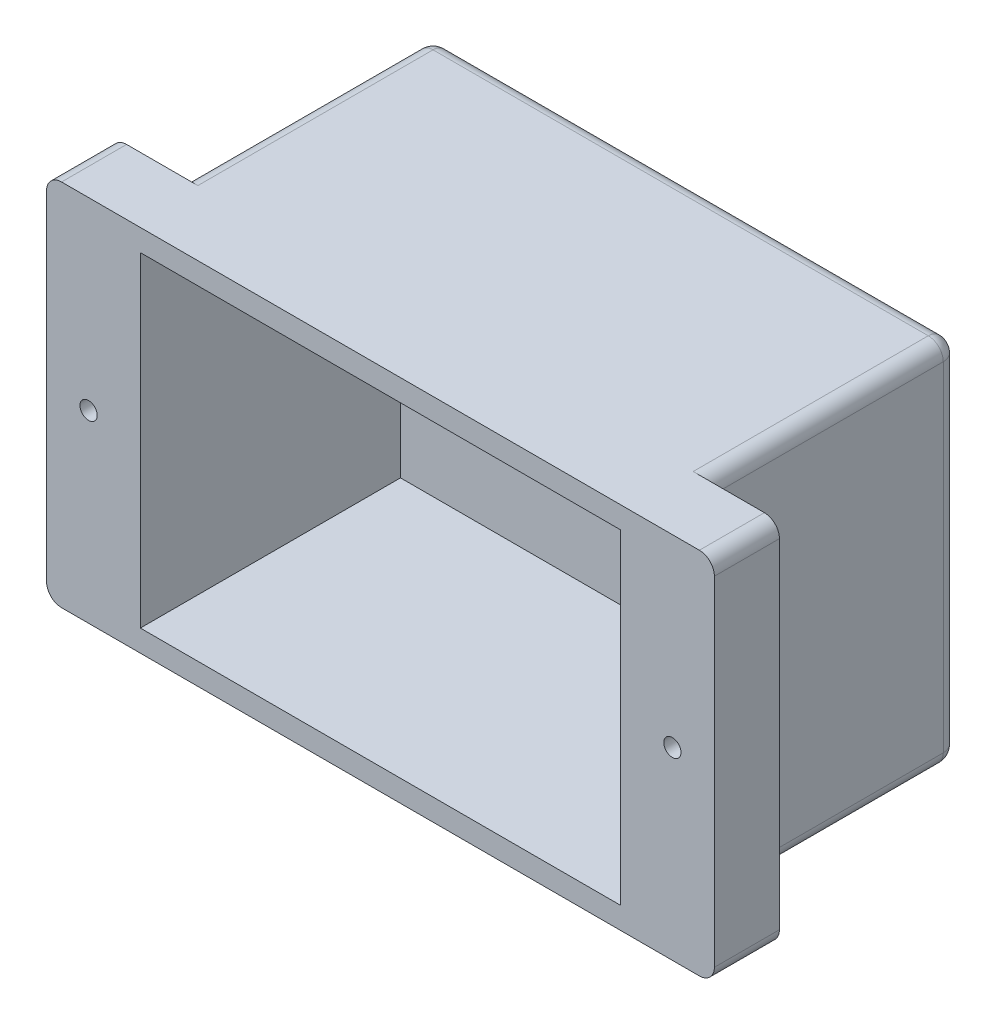
SolidWorks part; units mm, degrees
ref_plane "Front Plane" through (0, 0, 0) normal (0, 0, 1) x (1, 0, 0)
ref_plane "Top Plane" through (0, 0, 0) normal (0, 1, 0) x (1, 0, 0)
ref_plane "Right Plane" through (0, 0, 0) normal (1, 0, 0) x (0, 0, -1)
sketch "Sketch1" plane through (0, 0, 0) normal (0, 0, 1) x (1, 0, 0)
  line L0 (58.35, 0) -> (-58.35, 0) construction
  line L1 (66.75, -36.85) -> (-66.75, -36.85)
  line L2 (66.75, -36.85) -> (66.75, 36.85)
  line L3 (66.75, 36.85) -> (-66.75, 36.85)
  line L4 (-66.75, -36.85) -> (-66.75, 36.85)
  line L5 (66.75, -36.85) -> (-66.75, 36.85) construction
  line L6 (66.75, 36.85) -> (-66.75, -36.85) construction
  line L7 (-58.35, -1.725) -> (-58.35, 1.725) construction
  circle A0 centre (-58.35, 0) radius 1.725
  circle A1 centre (58.35, 0) radius 1.725
  point P0 (0, 0)
  point P9 (0, 0)
  point P11 (-58.35, -21.85)
  point P16 (-58.35, 21.85)
  point P24 (-58.35, 0)
  dimension "D4" = 3.45
  dimension "D1" = 133.5
  dimension "D2" = 73.7
  dimension "D3" = 116.7
extrude "Boss-Extrude1" add sketch "Sketch1" along normal blind 7.5 and the other way blind 5.5
sketch "Sketch2" plane through (0, 0, -5.5) normal (0, 0, -1) x (-1, 0, 0)
  line L0 (-66.75, 36.85) -> (66.75, 36.85) construction
  line L1 (52.5, -36.85) -> (-52.5, -36.85)
  line L2 (52.5, -36.85) -> (52.5, 36.85)
  line L3 (52.5, 36.85) -> (-52.5, 36.85)
  line L4 (-52.5, -36.85) -> (-52.5, 36.85)
  line L5 (52.5, -36.85) -> (-52.5, 36.85) construction
  line L6 (52.5, 36.85) -> (-52.5, -36.85) construction
  point P0 (0, 0)
  dimension "D1" = 105
extrude "Boss-Extrude2" add sketch "Sketch2" along normal blind 50
sketch "Sketch3" plane through (0, 0, 7.5) normal (0, 0, 1) x (1, 0, 0)
  line L0 (0, -1.75) -> (0, 1.75) construction
  line L6 (48.4799, 33.85) -> (40.85, 33.85)
  line L19 (50.35, 0) -> (-50.35, 0) construction
  line L20 (-38.95, 33.85) -> (-38.95, 27.35)
  line L21 (-50.35, 33.85) -> (-40.95, 33.85)
  line L22 (-50.35, 33.85) -> (-50.35, 1.75)
  line L24 (-40.95, 33.85) -> (-40.95, 27.35)
  line L25 (-38.95, 33.85) -> (-29.55, 33.85)
  line L26 (-29.55, 33.85) -> (-29.55, 27.35)
  line L40 (-27.55, 33.85) -> (-27.55, 27.35)
  line L41 (-27.55, 33.85) -> (-18.15, 33.85)
  line L75 (-18.15, 33.85) -> (-18.15, 27.35)
  line L77 (-16.15, 33.85) -> (-16.15, 27.35)
  line L93 (-16.15, 33.85) -> (-6.75, 33.85)
  line L94 (-6.75, 33.85) -> (-6.75, 27.35)
  line L96 (-4.75, 33.85) -> (-4.75, 27.35)
  line L98 (-4.75, 33.85) -> (4.65, 33.85)
  line L99 (4.65, 33.85) -> (4.65, 27.35)
  line L101 (6.65, 33.85) -> (6.65, 27.35)
  line L102 (6.65, 33.85) -> (16.05, 33.85)
  line L103 (16.05, 33.85) -> (16.05, 27.35)
  line L105 (18.05, 33.85) -> (18.05, 27.35)
  line L106 (18.05, 33.85) -> (27.45, 33.85)
  line L107 (27.45, 33.85) -> (27.45, 27.35)
  line L109 (29.45, 33.85) -> (29.45, 27.35)
  line L110 (29.45, 33.85) -> (38.85, 33.85)
  line L111 (38.85, 33.85) -> (38.85, 27.35)
  line L113 (40.85, 33.85) -> (40.85, 27.35)
  line L114 (40.85, 33.85) -> (50.25, 33.85)
  line L115 (50.25, 33.85) -> (50.25, 1.75)
  line L118 (2.9667, -1.75) -> (-5.3771, 1.75) construction
  line L119 (3.1755, 1.75) -> (-3.1755, -1.75) construction
  line L155 (-40.95, 27.35) -> (-38.95, 27.35)
  line L165 (-50.35, 1.75) -> (-50.35, 33.85)
  line L166 (-29.55, 27.35) -> (-27.55, 27.35)
  line L167 (-18.15, 27.35) -> (-16.15, 27.35)
  line L168 (-6.75, 27.35) -> (-4.75, 27.35)
  line L169 (4.65, 27.35) -> (6.65, 27.35)
  line L170 (16.05, 27.35) -> (18.05, 27.35)
  line L171 (27.45, 27.35) -> (29.45, 27.35)
  line L173 (38.85, 27.35) -> (40.85, 27.35)
  line L174 (-50.35, 1.75) -> (50.25, 1.75)
  line L175 (-50.35, -1.75) -> (50.25, -1.75)
  line L176 (-40.95, 33.85) -> (-50.35, 33.85)
  line L177 (-29.55, 33.85) -> (-38.95, 33.85)
  line L178 (-18.15, 33.85) -> (-27.55, 33.85)
  line L179 (-6.75, 33.85) -> (-16.15, 33.85)
  line L180 (4.65, 33.85) -> (-4.75, 33.85)
  line L181 (16.05, 33.85) -> (6.65, 33.85)
  line L182 (27.45, 33.85) -> (18.05, 33.85)
  line L183 (38.85, 33.85) -> (29.45, 33.85)
  point P0 (0, 0)
  point P2 (0, 0)
  point P10 (0, 0)
  point P11 (0, 0)
  point P14 (0, 0)
  point P42 (0, 0)
  point P45 (0, 0)
  dimension "D2" = 32.1
  dimension "D3" = 9.4
  dimension "D4" = 2
  dimension "D5" = 9
  dimension "D7" = 6.5
  dimension "D6" = 50.35
  dimension "D15" = 3.5
  dimension "D18" = 100.7
extrude "Cut-Extrude1" [suppressed] cut sketch "Sketch3" against normal blind 32.5 contours L22 L174 L115 L6 L113 L173 L111 L110 L109 L171 L107 L106 L105 L170 L103 L102 L101 L169 L99 L98 L96 L168 L94 L93 L77 L167 L75 L41 L40 L166 L26 L25 L20 L155 L24 L21
mirror "Mirror1" [suppressed] about plane through (0, 0, 0) normal (0, 1, 0)
sketch "Sketch4" [suppressed] plane through (0, 0, 7.85) normal (0, 0, 1) x (1, 0, 0)
  line L0 (-50.35, 1.75) -> (50.25, 1.75) construction
  line L1 (-40.95, 1.75) -> (-38.95, 1.75)
  line L2 (-40.95, 1.75) -> (-40.95, 8.25)
  line L3 (-40.95, 8.25) -> (-38.95, 8.25)
  line L4 (-38.95, 1.75) -> (-38.95, 8.25)
  line L5 (-40.95, 33.85) -> (-40.95, 27.35) construction
  line L6 (-29.55, 1.75) -> (-29.55, 8.25)
  line L7 (-29.55, 1.75) -> (-27.55, 1.75)
  line L8 (-27.55, 1.75) -> (-27.55, 8.25)
  line L9 (-29.55, 8.25) -> (-27.55, 8.25)
  line L10 (-18.15, 1.75) -> (-18.15, 8.25)
  line L11 (-18.15, 1.75) -> (-16.15, 1.75)
  line L12 (-16.15, 1.75) -> (-16.15, 8.25)
  line L13 (-18.15, 8.25) -> (-16.15, 8.25)
  line L14 (-6.75, 1.75) -> (-6.75, 8.25)
  line L15 (-6.75, 1.75) -> (-4.75, 1.75)
  line L16 (-4.75, 1.75) -> (-4.75, 8.25)
  line L17 (-6.75, 8.25) -> (-4.75, 8.25)
  line L18 (4.65, 1.75) -> (4.65, 8.25)
  line L19 (4.65, 1.75) -> (6.65, 1.75)
  line L20 (6.65, 1.75) -> (6.65, 8.25)
  line L21 (4.65, 8.25) -> (6.65, 8.25)
  line L22 (16.05, 1.75) -> (16.05, 8.25)
  line L23 (16.05, 1.75) -> (18.05, 1.75)
  line L24 (18.05, 1.75) -> (18.05, 8.25)
  line L25 (16.05, 8.25) -> (18.05, 8.25)
  line L26 (27.45, 1.75) -> (27.45, 8.25)
  line L27 (27.45, 1.75) -> (29.45, 1.75)
  line L28 (29.45, 1.75) -> (29.45, 8.25)
  line L29 (27.45, 8.25) -> (29.45, 8.25)
  line L30 (38.85, 1.75) -> (38.85, 8.25)
  line L31 (38.85, 1.75) -> (40.85, 1.75)
  line L32 (40.85, 1.75) -> (40.85, 8.25)
  line L33 (38.85, 8.25) -> (40.85, 8.25)
  dimension "D1" = 2
  dimension "D2" = 6.5
  dimension "D4" = 9.4
  dimension "D3" = 8
extrude "Boss-Extrude3" [suppressed] add sketch "Sketch4" against normal up to surface (32.5 mm away)
mirror "Mirror2" [suppressed] about plane through (0, 0, 0) normal (0, 1, 0)
sketch "Sketch5" [suppressed] plane through (0, 0, 7.85) normal (0, 0, 1) x (1, 0, 0)
  line L0 (-40.95, -8.25) -> (-40.95, -1.75) construction
  line L1 (-50.35, -1.75) -> (-40.95, -1.75)
  line L2 (-50.35, -1.75) -> (-50.35, -1.25)
  line L3 (-50.35, -1.25) -> (-40.95, -1.25)
  line L4 (-40.95, -1.75) -> (-40.95, -1.25)
  line L5 (-38.95, -1.75) -> (-38.95, -1.25)
  line L6 (-38.95, -1.75) -> (-29.55, -1.75)
  line L7 (-29.55, -1.75) -> (-29.55, -1.25)
  line L8 (-38.95, -1.25) -> (-29.55, -1.25)
  line L9 (-27.55, -1.75) -> (-27.55, -1.25)
  line L10 (-27.55, -1.75) -> (-18.15, -1.75)
  line L11 (-18.15, -1.75) -> (-18.15, -1.25)
  line L12 (-27.55, -1.25) -> (-18.15, -1.25)
  line L13 (-16.15, -1.75) -> (-16.15, -1.25)
  line L14 (-16.15, -1.75) -> (-6.75, -1.75)
  line L15 (-6.75, -1.75) -> (-6.75, -1.25)
  line L16 (-16.15, -1.25) -> (-6.75, -1.25)
  line L17 (-4.75, -1.75) -> (-4.75, -1.25)
  line L18 (-4.75, -1.75) -> (4.65, -1.75)
  line L19 (4.65, -1.75) -> (4.65, -1.25)
  line L20 (-4.75, -1.25) -> (4.65, -1.25)
  line L21 (6.65, -1.75) -> (6.65, -1.25)
  line L22 (6.65, -1.75) -> (16.05, -1.75)
  line L23 (16.05, -1.75) -> (16.05, -1.25)
  line L24 (6.65, -1.25) -> (16.05, -1.25)
  line L25 (18.05, -1.75) -> (18.05, -1.25)
  line L26 (18.05, -1.75) -> (27.45, -1.75)
  line L27 (27.45, -1.75) -> (27.45, -1.25)
  line L28 (18.05, -1.25) -> (27.45, -1.25)
  line L29 (29.45, -1.75) -> (29.45, -1.25)
  line L30 (29.45, -1.75) -> (38.85, -1.75)
  line L31 (38.85, -1.75) -> (38.85, -1.25)
  line L32 (29.45, -1.25) -> (38.85, -1.25)
  line L33 (40.85, -1.75) -> (40.85, -1.25)
  line L34 (40.85, -1.75) -> (50.25, -1.75)
  line L35 (50.25, -1.75) -> (50.25, -1.25)
  line L36 (40.85, -1.25) -> (50.25, -1.25)
  dimension "D1" = 0.5
  dimension "D3" = 2
  dimension "D2" = 9
extrude "Cut-Extrude2" [suppressed] cut sketch "Sketch5" against normal up to surface (32.5 mm away)
fillet "Fillet1" [suppressed] radius 5
fillet "Fillet3" [suppressed] radius 1
fillet "Fillet4" [suppressed] radius 1
sketch "Sketch6" plane through (0, 0, 7.5) normal (0, 0, 1) x (1, 0, 0)
  line L1 (48, -32.5) -> (-48, -32.5)
  line L2 (48, -32.5) -> (48, 32.5)
  line L3 (48, 32.5) -> (-48, 32.5)
  line L4 (-48, -32.5) -> (-48, 32.5)
  line L5 (48, -32.5) -> (-48, 32.5) construction
  line L6 (48, 32.5) -> (-48, -32.5) construction
  point P0 (0, 0)
  dimension "D1" = 65
  dimension "D2" = 96
extrude "Cut-Extrude3" cut sketch "Sketch6" against normal blind 52
fillet "Fillet5" radius 3 4 edges at (66.75, -36.85, 1) (-66.75, -36.85, 1) (-66.75, 36.85, 1) (66.75, 36.85, 1)
fillet "Fillet6" radius 3 8 edges at (0, 36.85, -55.5) (-52.5, 0, -55.5) (0, -36.85, -55.5) (52.5, 0, -55.5) (52.5, -36.85, -30.5) (-52.5, -36.85, -30.5) (-52.5, 36.85, -30.5) (52.5, 36.85, -30.5)
